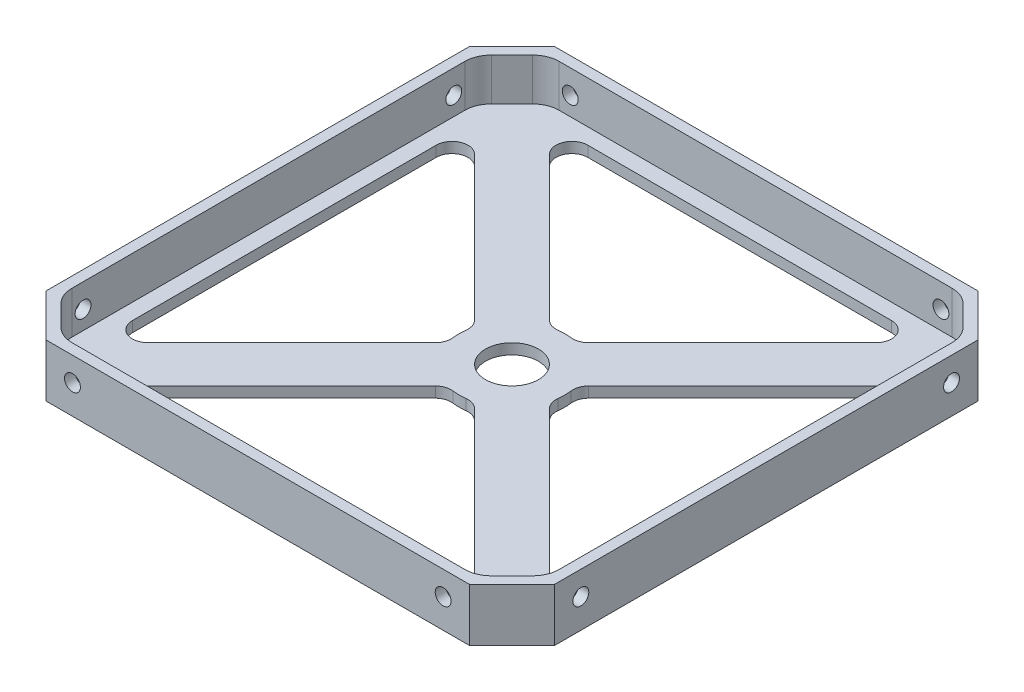
SolidWorks part; units mm, degrees
material "6061-T6 (SS)"
ref_plane "Front Plane" through (0, 0, 0) normal (0, 0, 1) x (1, 0, 0)
ref_plane "Top Plane" through (0, 0, 0) normal (0, 1, 0) x (1, 0, 0)
ref_plane "Right Plane" through (0, 0, 0) normal (1, 0, 0) x (0, 0, -1)
sketch "Sketch1" plane through (0, 0, 0) normal (0, 1, 0) x (1, 0, 0)
  line L0 (0, 8) -> (8, 0)
  line L1 (0, 0) -> (96, 0)
  line L2 (0, 0) -> (0, 96)
  line L3 (0, 96) -> (96, 96)
  line L4 (96, 0) -> (96, 96)
  line L5 (48, 96) -> (48, 0) construction
  line L6 (0, 48) -> (96, 48) construction
  line L7 (96, 8) -> (88, 0)
  line L8 (96, 88) -> (88, 96)
  line L9 (0, 88) -> (8, 96)
  dimension "D1" = 96
  dimension "D2" = 96
  dimension "D3" = 8
  dimension "D4" = 8
extrude "Boss-Extrude1" add sketch "Sketch1" along normal blind 10 contours L9 L2 L0 L1 L7 L4 L8 L3
shell "Shell1" thickness 2
sketch "Sketch2" plane through (0, 0, 0) normal (0, -1, 0) x (-1, 0, 0)
  line L0 (-4, 92) -> (-92, 4) construction
  line L1 (0, 88) -> (-8, 96) construction
  line L2 (-96, 8) -> (-88, 0) construction
  line L3 (-92, 92) -> (-4, 4) construction
  line L4 (-96, 88) -> (-88, 96) construction
  line L5 (0, 8) -> (-8, 0) construction
  line L6 (-5, 91) -> (-91, 91) construction
  line L7 (-91, 91) -> (-91, 5) construction
  line L8 (-91, 5) -> (-5, 5) construction
  line L9 (-5, 5) -> (-5, 91) construction
  line L10 (-8, 96) -> (-88, 96) construction
  line L12 (-12.0711, 91) -> (-91, 12.0711)
  line L13 (-5, 83.9289) -> (-83.9289, 5)
  line L14 (-5, 12.0711) -> (-83.9289, 91)
  line L15 (-12.0711, 5) -> (-91, 83.9289)
  line L16 (-5, 83.9289) -> (-5, 12.0711)
  line L17 (-12.0711, 5) -> (-83.9289, 5)
  line L18 (-91, 12.0711) -> (-91, 83.9289)
  line L19 (-83.9289, 91) -> (-12.0711, 91)
  circle A0 centre (-48, 48) radius 10
  circle A1 centre (-48, 48) radius 5
  dimension "D6" = 20
  dimension "D7" = 10
  dimension "D1" = 5
  dimension "D2" = 10
  dimension "D3" = 5
  dimension "D4" = 10
  dimension "D5" = 5
extrude "Cut-Extrude1" cut sketch "Sketch2" against normal through all contours A0 L12 L19 L14 | A0 L14 L16 L13 | A0 L13 L17 L15 | A0 L15 L18 L12 | A1
fillet "Fillet1" radius 3 16 edges at (12.0711, 1, -5) (83.9289, 1, -5) (50.5882, 1, -38.3407) (38.3407, 1, -50.5882) (45.4118, 1, -38.3407) (57.6593, 1, -50.5882) (5, 1, -12.0711) (38.3407, 1, -45.4118) (50.5882, 1, -57.6593) (91, 1, -12.0711) (91, 1, -83.9289) (57.6593, 1, -45.4118) (45.4118, 1, -57.6593) (83.9289, 1, -91) (12.0711, 1, -91) (5, 1, -83.9289)
sketch "Sketch3" plane through (96, 0, 0) normal (1, 0, 0) x (0, 0, -1)
  line L0 (8, 0) -> (88, 0) construction
  line L2 (0, 10) -> (0, 0) construction
  circle A0 centre (83, 5.5) radius 1.5
  circle A1 centre (13, 5.5) radius 1.5
  dimension "D4" = 3
  dimension "D1" = 5.5
  dimension "D2" = 5.5
  dimension "D3" = 13
  dimension "D5" = 83
extrude "Cut-Extrude2" cut sketch "Sketch3" against normal through all
sketch "Sketch4" plane through (0, 0, 0) normal (0, 0, 1) x (1, 0, 0)
  line L0 (8, 0) -> (88, 0) construction
  line L3 (0, 10) -> (0, 0) construction
  circle A0 centre (83, 5.5) radius 1.5
  circle A1 centre (13, 5.5) radius 1.5
  dimension "D2" = 3
  dimension "D1" = 5.5
  dimension "D3" = 13
  dimension "D4" = 83
  dimension "D5" = 5.5
extrude "Cut-Extrude3" cut sketch "Sketch4" against normal through all
fillet "Fillet2" radius 5 8 edges at (94, 6, -8.8284) (87.1716, 6, -2) (8.8284, 6, -2) (2, 6, -8.8284) (94, 6, -87.1716) (87.1716, 6, -94) (8.8284, 6, -94) (2, 6, -87.1716)
